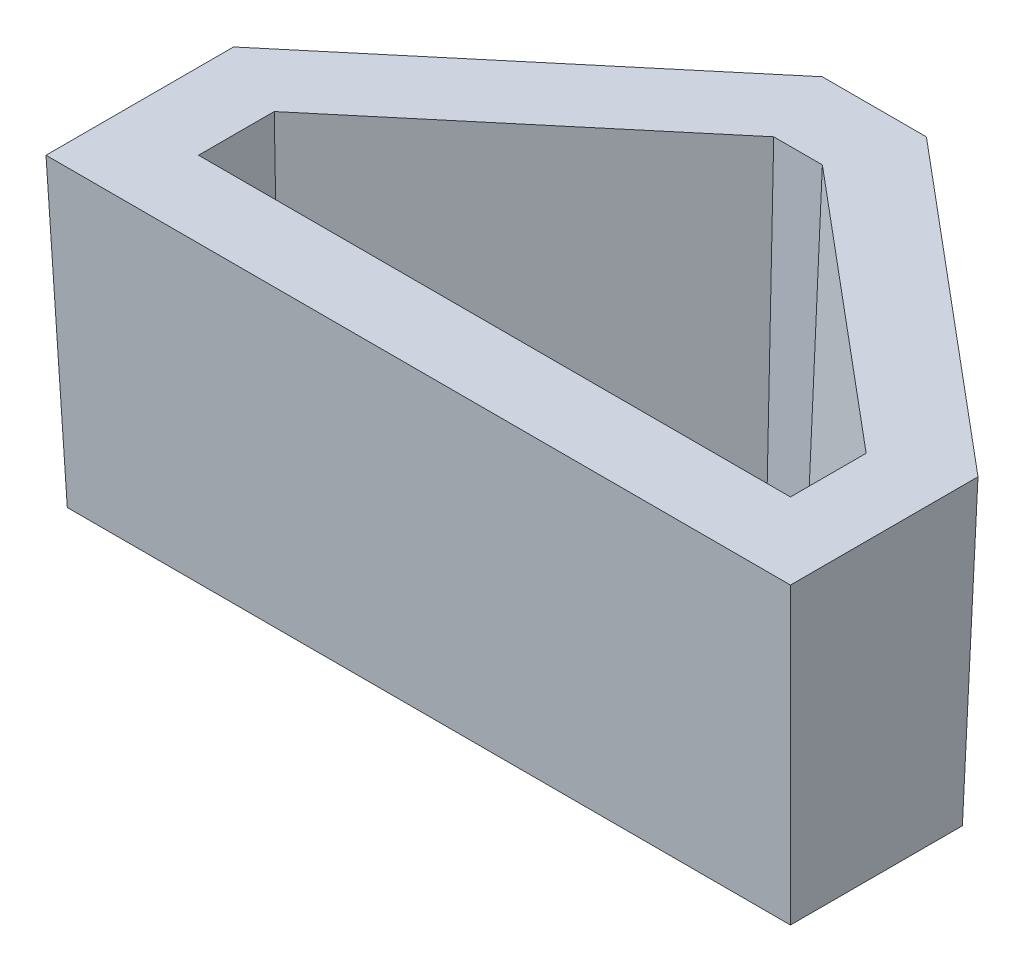
SolidWorks part; units mm, degrees
ref_plane "Alzado" through (0, 0, 0) normal (0, 0, 1) x (1, 0, 0)
ref_plane "Planta" through (0, 0, 0) normal (0, 1, 0) x (1, 0, 0)
ref_plane "Vista lateral" through (0, 0, 0) normal (1, 0, 0) x (0, 0, -1)
sketch "Croquis1" plane through (0, 0, 0) normal (0, 1, 0) x (1, 0, 0)
  line L0 (0, 0) -> (98.55, 0)
  line L1 (98.55, 0) -> (98.55, 12.6)
  line L2 (98.55, 12.6) -> (53.325, 50.5373)
  line L3 (53.325, 50.5373) -> (45.225, 50.5373)
  line L4 (45.225, 50.5373) -> (0, 12.6)
  line L5 (0, 12.6) -> (0, 0)
  point P7 (49.275, 50.5373)
  point P8 (49.275, 0)
  dimension "D1" = 98.55
  dimension "D2" = 8.1
  dimension "D3" = 59.03
  dimension "D4" = 59.03
  dimension "D5" = 12.6
extrude "Saliente-Extruir1" add sketch "Croquis1" against normal blind 2.54
sketch "Croquis2" plane through (0, 0, 0) normal (0, 1, 0) x (1, 0, 0)
  line L12 (-12.7, 18.5232) -> (-12.7, -12.7)
  line L13 (-12.7, -12.7) -> (111.25, -12.7)
  line L14 (111.25, -12.7) -> (111.25, 18.5232)
  line L15 (111.25, 18.5232) -> (57.9464, 63.2373)
  line L16 (57.9464, 63.2373) -> (40.6036, 63.2373)
  line L17 (40.6036, 63.2373) -> (-12.7, 18.5232)
  line L18 (-12.7, 18.5232) -> (-12.7, -12.7)
  line L19 (-12.7, -12.7) -> (111.25, -12.7)
  line L20 (111.25, -12.7) -> (111.25, 18.5232)
  line L21 (111.25, 18.5232) -> (57.9464, 63.2373)
  line L22 (57.9464, 63.2373) -> (40.6036, 63.2373)
  line L23 (40.6036, 63.2373) -> (-12.7, 18.5232)
  dimension "D1" = 12.7
extrude "Saliente-Extruir2" add sketch "Croquis2" against normal blind 50.8 draft 2
sketch "Croquis3" plane through (0, 0, 0) normal (0, 1, 0) x (1, 0, 0)
  line L6 (0, 0) -> (98.55, 0)
  line L7 (98.55, 0) -> (98.55, 12.6)
  line L8 (98.55, 12.6) -> (53.325, 50.5373)
  line L9 (53.325, 50.5373) -> (45.225, 50.5373)
  line L10 (45.225, 50.5373) -> (0, 12.6)
  line L11 (0, 12.6) -> (0, 0)
  line L12 (0, 0) -> (98.55, 0)
  line L13 (98.55, 0) -> (98.55, 12.6)
  line L14 (98.55, 12.6) -> (53.325, 50.5373)
  line L15 (53.325, 50.5373) -> (45.225, 50.5373)
  line L16 (45.225, 50.5373) -> (0, 12.6)
  line L17 (0, 12.6) -> (0, 0)
  dimension "D1" = 0
extrude "Cortar-Extruir1" cut sketch "Croquis3" against normal blind 50.8 draft 2
sketch "Croquis5" plane through (0, 0, 0) normal (0, 1, 0) x (1, 0, 0)
  line L2 (53.325, 50.5373) -> (45.225, 50.5373) construction
  line L7 (40.6036, 63.2373) -> (-12.7, 18.5232)
  line L8 (-12.7, 18.5232) -> (-12.7, -12.7)
  line L9 (-12.7, -12.7) -> (111.25, -12.7)
  line L10 (111.25, -12.7) -> (111.25, 18.5232)
  line L11 (111.25, 18.5232) -> (57.9464, 63.2373)
  line L12 (57.9464, 63.2373) -> (40.6036, 63.2373)
  line L13 (40.6036, 63.2373) -> (-12.7, 18.5232)
  line L14 (-12.7, 18.5232) -> (-12.7, -12.7)
  line L15 (-12.7, -12.7) -> (111.25, -12.7)
  line L16 (111.25, -12.7) -> (111.25, 18.5232)
  line L17 (111.25, 18.5232) -> (57.9464, 63.2373)
  line L18 (57.9464, 63.2373) -> (40.6036, 63.2373)
  dimension "D1" = 0
sketch "Croquis6" plane through (0, -50.8, 0) normal (0, -1, 0) x (1, 0, 0)
  line L6 (-10.926, -17.6958) -> (41.2491, -61.4633)
  line L7 (41.2491, -61.4633) -> (57.3009, -61.4633)
  line L8 (57.3009, -61.4633) -> (109.476, -17.6958)
  line L9 (109.476, -17.6958) -> (109.476, 10.926)
  line L10 (109.476, 10.926) -> (-10.926, 10.926)
  line L11 (-10.926, 10.926) -> (-10.926, -17.6958)
  line L12 (-10.926, -17.6958) -> (41.2491, -61.4633)
  line L13 (41.2491, -61.4633) -> (57.3009, -61.4633)
  line L14 (57.3009, -61.4633) -> (109.476, -17.6958)
  line L15 (109.476, -17.6958) -> (109.476, 10.926)
  line L16 (109.476, 10.926) -> (-10.926, 10.926)
  line L17 (-10.926, 10.926) -> (-10.926, -17.6958)
  dimension "D1" = 0
